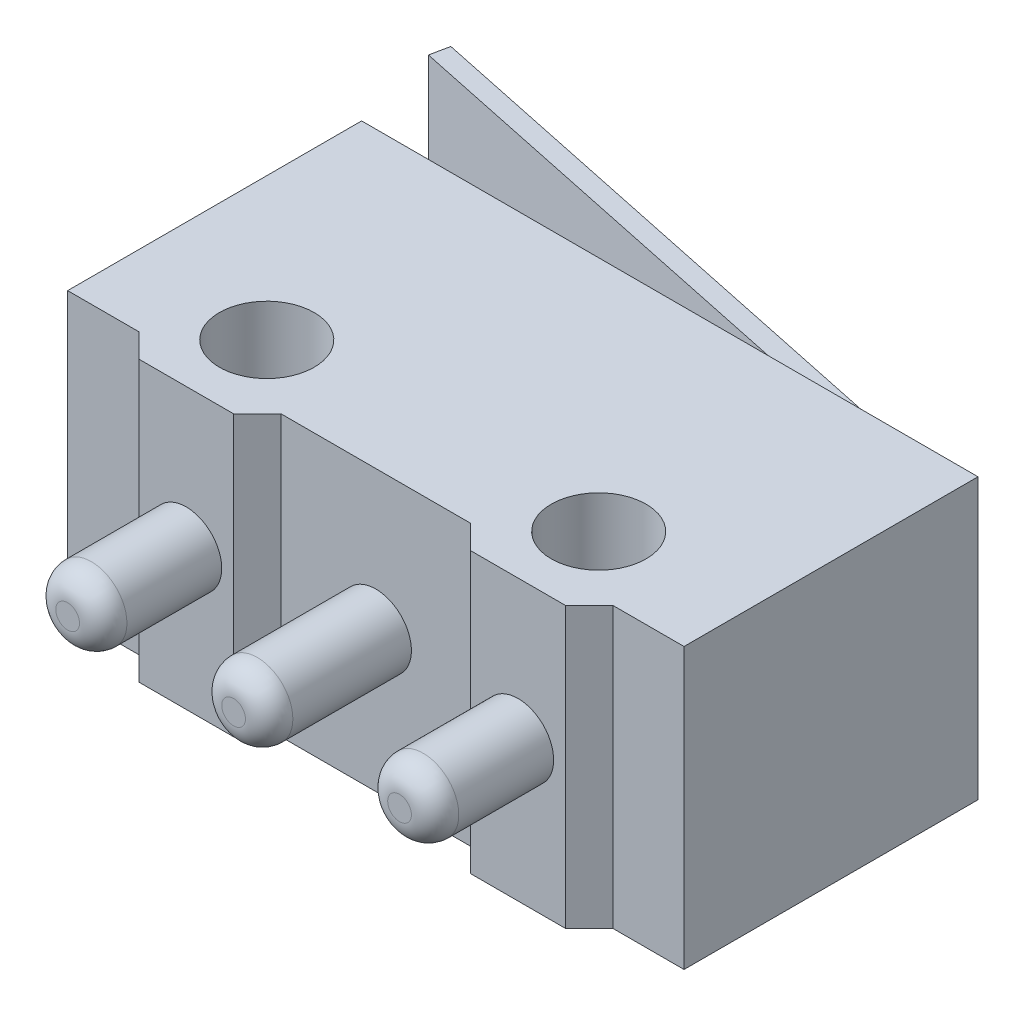
SolidWorks part; units mm, degrees
material "ABS"
ref_plane "Front Plane" through (0, 0, 0) normal (0, 0, 1) x (1, 0, 0)
ref_plane "Top Plane" through (0, 0, 0) normal (0, 1, 0) x (1, 0, 0)
ref_plane "Right Plane" through (0, 0, 0) normal (1, 0, 0) x (0, 0, -1)
sketch "Sketch1" plane through (0, 0, 0) normal (0, 1, 0) x (1, 0, 0)
  line L0 (0, 6.2373) -> (0, -4.4682) construction
  line L1 (-6.5, -3.1) -> (-5, -3.1)
  line L2 (-6.5, -3.1) -> (-6.5, 3.1)
  line L3 (-6.5, 3.1) -> (3.9559, 3.1)
  line L4 (6.5, -3.1) -> (6.5, 3.1)
  line L5 (-6.5, -3.1) -> (6.5, 3.1) construction
  line L6 (-6.5, 3.1) -> (6.5, -3.1) construction
  line L7 (3.5, -4.4182) -> (3.5, 0.05) construction
  line L8 (2.5, -3.6) -> (2, -3.1)
  line L9 (4.5, -3.6) -> (2.5, -3.6)
  line L10 (4.5, -3.6) -> (5, -3.1)
  line L11 (5, -3.1) -> (6.5, -3.1)
  line L12 (-2.5, -3.6) -> (-2, -3.1)
  line L13 (-4.5, -3.6) -> (-2.5, -3.6)
  line L14 (-4.5, -3.6) -> (-5, -3.1)
  line L15 (-2, -3.1) -> (2, -3.1)
  line L16 (5.9, 3.1) -> (-7.4177, 5.9)
  line L17 (-7.4177, 5.9) -> (-7.5, 5.5086)
  line L18 (-7.5, 5.5086) -> (3.9559, 3.1)
  line L19 (5.9, 3.1) -> (6.5, 3.1)
  circle A0 centre (3.5, -1.9) radius 1
  circle A1 centre (-3.5, -1.9) radius 1
  point P0 (0, 0)
  dimension "D3" = 2
  dimension "D1" = 13
  dimension "D2" = 6.2
  dimension "D4" = 3
  dimension "D5" = 0.5
  dimension "D6" = 5
  dimension "D7" = 2
  dimension "D8" = 135
  dimension "D9" = 14
  dimension "D10" = 9
  dimension "D11" = 0.4
  dimension "D12" = 0.6
extrude "Boss-Extrude1" add sketch "Sketch1" along normal mid plane 5.9
sketch "Sketch2" plane through (0, 2.95, 0) normal (0, 1, 0) x (1, 0, 0)
  line L0 (5.9, 3.1) -> (3.9559, 3.1)
  line L16 (6.5, 3.1) -> (5.9, 3.1)
  line L17 (5.9, 3.1) -> (-7.4177, 5.9)
  line L18 (-7.4177, 5.9) -> (-7.5, 5.5086)
  line L19 (-7.5, 5.5086) -> (3.9559, 3.1)
  line L20 (3.9559, 3.1) -> (-6.5, 3.1)
  line L21 (-6.5, 3.1) -> (-6.5, -3.1)
  line L22 (-6.5, -3.1) -> (-5, -3.1)
  line L23 (-5, -3.1) -> (-4.5, -3.6)
  line L24 (-4.5, -3.6) -> (-2.5, -3.6)
  line L25 (-2.5, -3.6) -> (-2, -3.1)
  line L26 (-2, -3.1) -> (2, -3.1)
  line L27 (2, -3.1) -> (2.5, -3.6)
  line L28 (2.5, -3.6) -> (4.5, -3.6)
  line L29 (4.5, -3.6) -> (5, -3.1)
  line L30 (5, -3.1) -> (6.5, -3.1)
  line L31 (6.5, -3.1) -> (6.5, 3.1)
  line L33 (5.9, 3.1) -> (-7.4177, 5.9)
  line L34 (-7.4177, 5.9) -> (-7.5, 5.5086)
  line L35 (-7.5, 5.5086) -> (3.9559, 3.1)
  dimension "D1" = 0
extrude "Cut-Extrude1" cut sketch "Sketch2" against normal blind 0.5
mirror "Mirror1" about plane through (0, 0, 0) normal (0, 1, 0) of "Cut-Extrude1"
sketch "Sketch3" plane through (0, 0, 3.1) normal (0, 0, 1) x (1, 0, 0)
  line L0 (0, 0) -> (0, 3.0921) construction
  line L1 (-4.5, 2.95) -> (-2.5, 2.95) construction
  circle A0 centre (0, 0) radius 0.75
  circle A1 centre (-3.5, 0) radius 0.75
  circle A2 centre (3.5, 0) radius 0.75
  point P10 (-3.5, 2.95)
  dimension "D1" = 1.5
extrude "Boss-Extrude2" add sketch "Sketch3" along normal blind 3
fillet "Fillet1" radius 0.5 3 edges at (2.75, 0, 6.1) (0.75, 0, 6.1) (-2.75, 0, 6.1)
